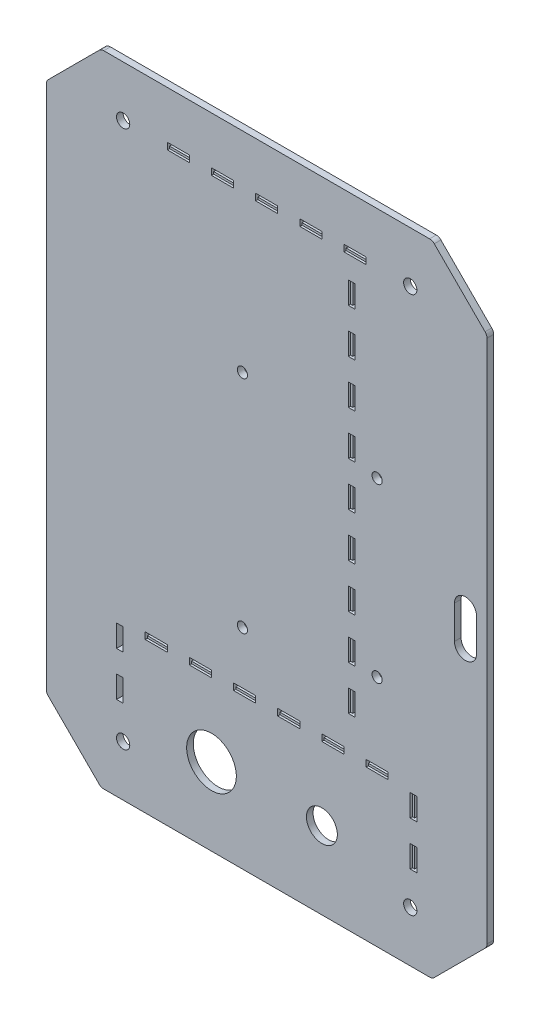
SolidWorks part; units mm, degrees
other "Marquage1"
sketch "Esquisse11" plane through (99.7487, 144.7487, 0) normal (0.25, 0.1836, -0.9507) x (0.0259, -0.9828, -0.183)
ref_plane "Plan de face" through (0, 0, 0) normal (0, 0, 1) x (1, 0, 0)
ref_plane "Plan de dessus" through (0, 0, 0) normal (0, 1, 0) x (1, 0, 0)
ref_plane "Plan de droite" through (0, 0, 0) normal (1, 0, 0) x (0, 0, -1)
sketch "Esquisse1" plane through (0, 0, 0) normal (0, 0, 1) x (1, 0, 0)
  line L0 (-99.7487, 120) -> (-75, 144.7487)
  line L1 (-75, 144.7487) -> (75, 144.7487)
  line L2 (-99.7487, 120) -> (-99.7487, -120)
  line L3 (-75, -144.7487) -> (75, -144.7487)
  line L4 (99.7487, 120) -> (99.7487, -120)
  line L5 (75, 144.7487) -> (99.7487, 120)
  line L6 (99.7487, -120) -> (75, -144.7487)
  line L7 (-87.3744, 132.3744) -> (87.3744, -132.3744) construction
  line L8 (-99.7487, -120) -> (-75, -144.7487)
  line L9 (-87.3744, -132.3744) -> (87.3744, 132.3744) construction
  point P0 (0, 0)
  point P14 (0, 0)
  dimension "D1" = 240
  dimension "D2" = 150
  dimension "D3" = 35
  dimension "D4" = 135
  dimension "D5" = 135
extrude "Base" add sketch "Esquisse1" along normal blind 3
sketch "Esquisse2" plane through (0, 0, 3) normal (0, 0, 1) x (1, 0, 0)
  line L0 (-99.7487, 0) -> (99.7487, 0) construction
  line L1 (-99.7487, 120) -> (-99.7487, -120) construction
  line L2 (99.7487, -120) -> (99.7487, 120) construction
  line L3 (0, 144.7487) -> (0, -144.7487) construction
  line L4 (75, 144.7487) -> (-75, 144.7487) construction
  line L5 (-75, -144.7487) -> (75, -144.7487) construction
  line L11 (-67.1213, 123.8701) -> (-62.8787, 119.6274) construction
  line L12 (-67.1213, 119.6274) -> (-62.8787, 123.8701) construction
  circle A0 centre (-65, 121.7487) radius 3
  circle A1 centre (65, 121.7487) radius 3
  circle A2 centre (65, -121.7487) radius 3
  circle A3 centre (-65, -121.7487) radius 3
  point P12 (-65, 121.7487)
  dimension "D5" = 6
  dimension "D3" = 23
  dimension "D4" = 65
extrude "Perçage profilé" cut sketch "Esquisse2" against normal blind 5
sketch "Esquisse3" plane through (0, 0, 0) normal (0, 0, -1) x (-1, 0, 0)
  line L0 (45, 0) -> (-45, 0) construction
  line L6 (75, -144.7487) -> (-75, -144.7487) construction
  line L7 (45, 45) -> (45, -45) construction
  line L8 (45, -45) -> (-45, -45) construction
  line L9 (-45, -45) -> (-45, 45) construction
  line L10 (-45, 45) -> (45, 45) construction
  line L11 (-99.7487, -120) -> (-99.7487, 120) construction
  circle A4 centre (-50, 39) radius 2.3
  circle A5 centre (11, 50) radius 2.3
  circle A6 centre (-50, -39) radius 2.3
  circle A7 centre (11, -50) radius 2.3
  point P16 (-99.7487, 0)
  point P19 (0, -144.7487)
  point P20 (0, 0)
  point P22 (0, -45)
  dimension "D3" = 4.6
  dimension "D8" = 4.6
  dimension "D1" = 90
  dimension "D2" = 90
  dimension "D4" = 5
  dimension "D5" = 6
  dimension "D6" = 34
  dimension "D7" = 5
extrude "Perçage Lidar" cut sketch "Esquisse3" against normal through all
sketch "Esquisse4" plane through (0, 0, 0) normal (0, 0, -1) x (-1, 0, 0)
  line L0 (75, -144.7487) -> (-75, -144.7487) construction
  line L1 (0, -144.7487) -> (0, -86.7053) construction
  circle A0 centre (25, -109.7487) radius 11.25
  dimension "D1" = 22.5
  dimension "D2" = 35
  dimension "D3" = 25
extrude "Perçage bouton d'arret d'urgence" cut sketch "Esquisse4" against normal through all
sketch "Esquisse5" plane through (0, 0, 0) normal (0, 0, -1) x (-1, 0, 0)
  line L0 (0, -59.6223) -> (0, -144.7487) construction
  line L1 (75, -144.7487) -> (-75, -144.7487) construction
  circle A0 centre (-25, -109.7487) radius 7
  dimension "D1" = 14
  dimension "D2" = 25
  dimension "D3" = 35
extrude "Perçage tirette" cut sketch "Esquisse5" against normal through all
sketch "Esquisse7" plane through (0, 0, 0) normal (0, 0, -1) x (-1, 0, 0)
  line L6 (-90, 7.5) -> (-90, -7.5) construction
  line L7 (-85, 7.5) -> (-85, -7.5)
  line L8 (-95, 7.5) -> (-95, -7.5)
  line L9 (-99.7487, -120) -> (-99.7487, 120) construction
  arc A2 (-85, 7.5) -> (-95, 7.5) centre (-90, 7.5) ccw
  arc A3 (-95, -7.5) -> (-85, -7.5) centre (-90, -7.5) ccw
  circle A4 centre (-50, -39) radius 2.3 construction
  point P7 (-90, 0)
  point P23 (-99.7487, 0)
  dimension "D4" = 5
  dimension "D1" = 15
  dimension "D5" = 40
extrude "Perçage cable management" cut sketch "Esquisse7" against normal through all
sketch "Sketch1" plane through (0, 0, 0) normal (0, 0, -1) x (-1, 0, 0)
  line L0 (-45, 123.2487) -> (-35, 123.2487)
  line L1 (-45, 123.2487) -> (-45, 120.2487)
  line L2 (-45, 120.2487) -> (-35, 120.2487)
  line L3 (-35, 123.2487) -> (-35, 120.2487)
  line L4 (-75, 121.7487) -> (-55, 121.7487) construction
  line L5 (-45, 121.7487) -> (-35, 121.7487) construction
  line L6 (-25, 123.2487) -> (-25, 120.2487)
  line L7 (-25, 123.2487) -> (-15, 123.2487)
  line L8 (-15, 123.2487) -> (-15, 120.2487)
  line L9 (-25, 120.2487) -> (-15, 120.2487)
  line L10 (-5, 123.2487) -> (-5, 120.2487)
  line L11 (-5, 123.2487) -> (5, 123.2487)
  line L12 (5, 123.2487) -> (5, 120.2487)
  line L13 (-5, 120.2487) -> (5, 120.2487)
  line L14 (15, 123.2487) -> (15, 120.2487)
  line L15 (15, 123.2487) -> (25, 123.2487)
  line L16 (25, 123.2487) -> (25, 120.2487)
  line L17 (15, 120.2487) -> (25, 120.2487)
  line L18 (35, 123.2487) -> (35, 120.2487)
  line L19 (35, 123.2487) -> (45, 123.2487)
  line L20 (45, 123.2487) -> (45, 120.2487)
  line L21 (35, 120.2487) -> (45, 120.2487)
  line L22 (0, 0) -> (0, -37.251) construction
  line L23 (-68, -106.7487) -> (-65, -106.7487)
  line L24 (-68, -106.7487) -> (-68, -96.7487)
  line L25 (-68, -96.7487) -> (-65, -96.7487)
  line L26 (-65, -106.7487) -> (-65, -96.7487)
  line L27 (-66.5, -106.7487) -> (-66.5, -96.7487) construction
  line L28 (-40, 90.2487) -> (-40, 80.2487)
  line L29 (-40, 110.2487) -> (-37, 110.2487)
  line L30 (-68, -86.7487) -> (-68, -76.7487)
  line L31 (-68, -86.7487) -> (-65, -86.7487)
  line L32 (-65, -86.7487) -> (-65, -76.7487)
  line L33 (-68, -76.7487) -> (-65, -76.7487)
  line L34 (68, -86.7487) -> (65, -86.7487)
  line L35 (65, -86.7487) -> (65, -76.7487)
  line L36 (68, -76.7487) -> (65, -76.7487)
  line L37 (68, -86.7487) -> (68, -76.7487)
  line L38 (68, -96.7487) -> (65, -96.7487)
  line L39 (65, -106.7487) -> (65, -96.7487)
  line L40 (68, -106.7487) -> (65, -106.7487)
  line L41 (68, -106.7487) -> (68, -96.7487)
  line L42 (-35, -76.7487) -> (-35, -73.7487)
  line L43 (-55, -76.7487) -> (-45, -76.7487)
  line L44 (-55, -76.7487) -> (-55, -73.7487)
  line L45 (-55, -73.7487) -> (-45, -73.7487)
  line L46 (-45, -76.7487) -> (-45, -73.7487)
  line L47 (-35, -76.7487) -> (-25, -76.7487)
  line L48 (-25, -76.7487) -> (-25, -73.7487)
  line L49 (-35, -73.7487) -> (-25, -73.7487)
  line L50 (-15, -76.7487) -> (-15, -73.7487)
  line L51 (-15, -76.7487) -> (-5, -76.7487)
  line L52 (-5, -76.7487) -> (-5, -73.7487)
  line L53 (-15, -73.7487) -> (-5, -73.7487)
  line L54 (5, -76.7487) -> (5, -73.7487)
  line L55 (5, -76.7487) -> (15, -76.7487)
  line L56 (15, -76.7487) -> (15, -73.7487)
  line L57 (5, -73.7487) -> (15, -73.7487)
  line L58 (25, -76.7487) -> (25, -73.7487)
  line L59 (25, -76.7487) -> (35, -76.7487)
  line L60 (35, -76.7487) -> (35, -73.7487)
  line L61 (25, -73.7487) -> (35, -73.7487)
  line L62 (45, -76.7487) -> (45, -73.7487)
  line L63 (45, -76.7487) -> (55, -76.7487)
  line L64 (55, -76.7487) -> (55, -73.7487)
  line L65 (45, -73.7487) -> (55, -73.7487)
  line L66 (-40, 110.2487) -> (-40, 100.2487)
  line L67 (-40, 100.2487) -> (-37, 100.2487)
  line L68 (-37, 110.2487) -> (-37, 100.2487)
  line L69 (-40, 90.2487) -> (-37, 90.2487)
  line L70 (-37, 90.2487) -> (-37, 80.2487)
  line L71 (-40, 80.2487) -> (-37, 80.2487)
  line L72 (-40, 70.2487) -> (-40, 60.2487)
  line L73 (-40, 70.2487) -> (-37, 70.2487)
  line L74 (-37, 70.2487) -> (-37, 60.2487)
  line L75 (-40, 60.2487) -> (-37, 60.2487)
  line L76 (-40, 50.2487) -> (-40, 40.2487)
  line L77 (-40, 50.2487) -> (-37, 50.2487)
  line L78 (-37, 50.2487) -> (-37, 40.2487)
  line L79 (-40, 40.2487) -> (-37, 40.2487)
  line L80 (-40, 30.2487) -> (-40, 20.2487)
  line L81 (-40, 30.2487) -> (-37, 30.2487)
  line L82 (-37, 30.2487) -> (-37, 20.2487)
  line L83 (-40, 20.2487) -> (-37, 20.2487)
  line L84 (-40, 10.2487) -> (-40, 0.2487)
  line L85 (-40, 10.2487) -> (-37, 10.2487)
  line L86 (-37, 10.2487) -> (-37, 0.2487)
  line L87 (-40, 0.2487) -> (-37, 0.2487)
  line L88 (-40, -9.7513) -> (-40, -19.7513)
  line L89 (-40, -9.7513) -> (-37, -9.7513)
  line L90 (-37, -9.7513) -> (-37, -19.7513)
  line L91 (-40, -19.7513) -> (-37, -19.7513)
  line L92 (-40, -29.7513) -> (-40, -39.7513)
  line L93 (-40, -29.7513) -> (-37, -29.7513)
  line L94 (-37, -29.7513) -> (-37, -39.7513)
  line L95 (-40, -39.7513) -> (-37, -39.7513)
  line L96 (-40, -49.7513) -> (-40, -59.7513)
  line L97 (-40, -49.7513) -> (-37, -49.7513)
  line L98 (-37, -49.7513) -> (-37, -59.7513)
  line L99 (-40, -59.7513) -> (-37, -59.7513)
  point P53 (-100.1879, -120)
  dimension "D1" = 3
  dimension "D2" = 10
  dimension "D3" = 10
  dimension "D4" = 3
  dimension "D5" = 10
  dimension "D6" = 3
  dimension "D7" = 10
  dimension "D8" = 65
  dimension "D9" = 10
  dimension "D10" = 10
  dimension "D11" = 3
extrude "Cut-Extrude1" cut sketch "Sketch1" against normal through all
sketch "Esquisse8" plane through (0, 0, 3) normal (0, 0, 1) x (1, 0, 0)
  line L1 (-69.7487, 24.5) -> (-69.7487, -24.5) construction
  line L2 (-69.7487, 0) -> (-99.7487, 0) construction
  line L3 (-99.7487, 120) -> (-99.7487, -120) construction
  circle A0 centre (-69.7487, 24.5) radius 2.65
  circle A1 centre (-69.7487, -24.5) radius 2.65
  dimension "D1" = 5.3
  dimension "D2" = 5.3
  dimension "D3" = 49
  dimension "D4" = 30
sketch "Esquisse9" plane through (0, 0, 3) normal (0, 0, 1) x (1, 0, 0)
  line L0 (-53.7487, 17.25) -> (-53.7487, -17.25) construction
  line L1 (-99.7487, 0) -> (-53.7487, 0) construction
  line L2 (-99.7487, 120) -> (-99.7487, -120) construction
  circle A0 centre (-53.7487, 17.25) radius 2.1
  circle A1 centre (-53.7487, -17.25) radius 2.1
  point P11 (-53.7487, 0)
  dimension "D1" = 4.2
  dimension "D2" = 4.2
  dimension "D3" = 34.5
  dimension "D4" = 46
fillet "Congé1" radius 3 8 edges at (99.7487, -120, 1.5) (75, -144.7487, 1.5) (-75, -144.7487, 1.5) (-99.7487, -120, 1.5) (-99.7487, 120, 1.5) (-75, 144.7487, 1.5) (99.7487, 120, 1.5) (75, 144.7487, 1.5)
sketch "Esquisse10" plane through (0, 0, 0) normal (0, 0, -1) x (-1, 0, 0)
  line L0 (45, 120.2487) -> (45, 123.2487) construction
  line L1 (-45, 120.2487) -> (45, 120.2487)
  line L2 (-45, 120.2487) -> (-45, 121.2487)
  line L3 (-45, 121.2487) -> (45, 121.2487)
  line L4 (45, 120.2487) -> (45, 121.2487)
  line L5 (-40, -59.7513) -> (-37, -59.7513) construction
  line L6 (-37, 110.2487) -> (-38, 110.2487)
  line L7 (-37, 110.2487) -> (-37, -59.7513)
  line L8 (-37, -59.7513) -> (-38, -59.7513)
  line L9 (-38, 110.2487) -> (-38, -59.7513)
  line L10 (55, -76.7487) -> (55, -73.7487) construction
  line L11 (-55, -76.7487) -> (55, -76.7487)
  line L12 (-55, -76.7487) -> (-55, -75.7487)
  line L13 (-55, -75.7487) -> (55, -75.7487)
  line L14 (55, -76.7487) -> (55, -75.7487)
  line L15 (65, -106.7487) -> (68, -106.7487) construction
  line L16 (65, -76.7487) -> (66, -76.7487)
  line L17 (65, -76.7487) -> (65, -106.7487)
  line L18 (65, -106.7487) -> (66, -106.7487)
  line L19 (66, -76.7487) -> (66, -106.7487)
  line L20 (-68, -106.7487) -> (-65, -106.7487) construction
  line L21 (-65, -76.7487) -> (-66, -76.7487)
  line L22 (-65, -76.7487) -> (-65, -106.7487)
  line L23 (-65, -106.7487) -> (-66, -106.7487)
  line L24 (-66, -76.7487) -> (-66, -106.7487)
  dimension "D1" = 1
extrude "Boss.-Extru.1" add sketch "Esquisse10" against normal blind 2
